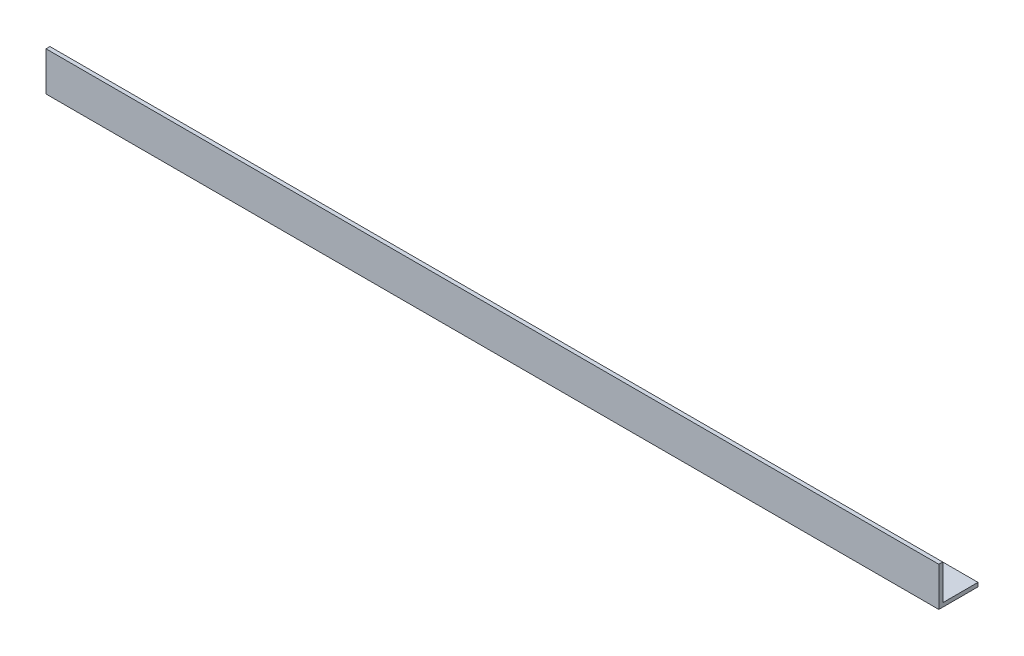
SolidWorks part; units mm, degrees
ref_plane "Спереди" through (0, 0, 0) normal (0, 0, 1) x (1, 0, 0)
ref_plane "Сверху" through (0, 0, 0) normal (0, 1, 0) x (1, 0, 0)
ref_plane "Справа" through (0, 0, 0) normal (1, 0, 0) x (0, 0, -1)
sketch "Эскиз1" plane through (0, 0, 0) normal (1, 0, 0) x (0, 0, -1)
  line L0 (0, 0) -> (0, 15)
  line L1 (0, 15) -> (1.5, 15)
  line L2 (1.5, 15) -> (1.5, 1.5)
  line L3 (1.5, 1.5) -> (15, 1.5)
  line L4 (15, 1.5) -> (15, 0)
  line L5 (15, 0) -> (0, 0)
  dimension "D1" = 15
  dimension "D2" = 15
  dimension "D3" = 1.5
  dimension "D4" = 1.5
extrude "Бобышка-Вытянуть1" add sketch "Эскиз1" along normal blind 342
